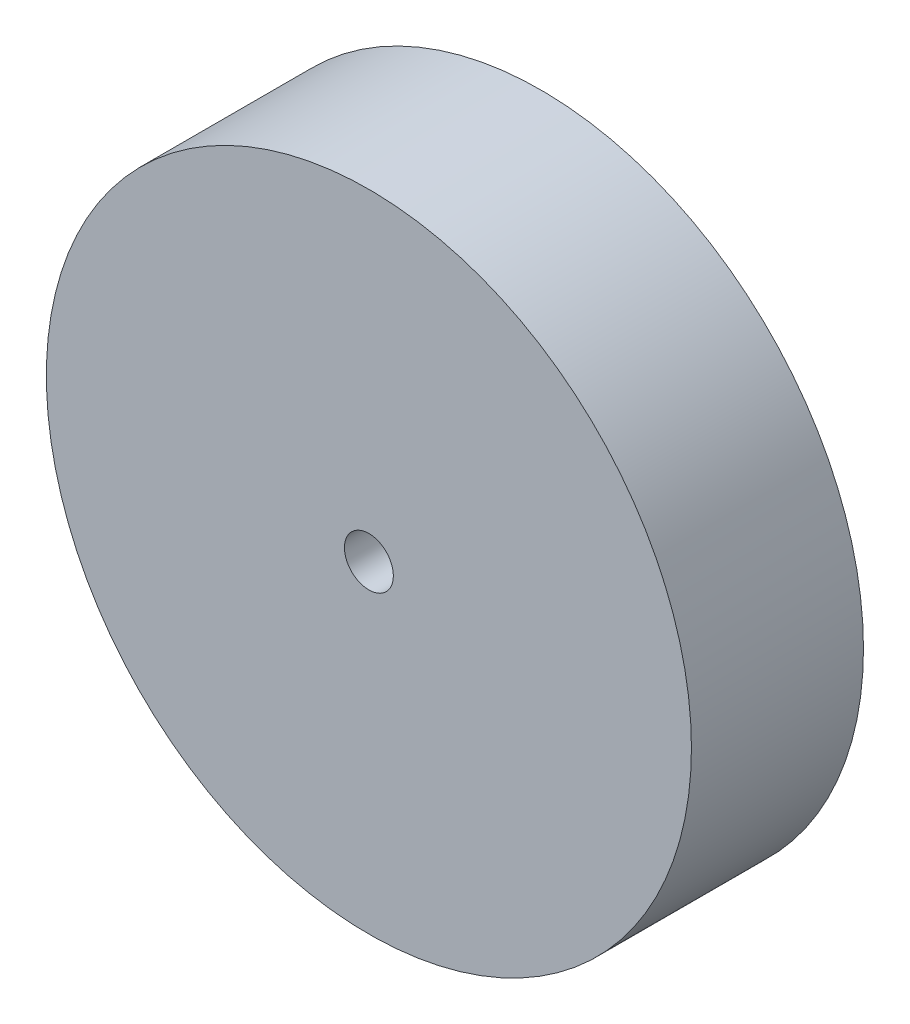
SolidWorks part; units mm, degrees
ref_plane "Front Plane" through (0, 0, 0) normal (0, 0, 1) x (1, 0, 0)
ref_plane "Top Plane" through (0, 0, 0) normal (0, 1, 0) x (1, 0, 0)
ref_plane "Right Plane" through (0, 0, 0) normal (1, 0, 0) x (0, 0, -1)
sketch "Sketch1" plane through (0, 0, 0) normal (0, 0, 1) x (1, 0, 0)
  circle A0 centre (0, 0) radius 75
  circle A1 centre (0, 0) radius 5.6859
  dimension "D1" = 150
extrude "Boss-Extrude1" add sketch "Sketch1" along normal blind 40
